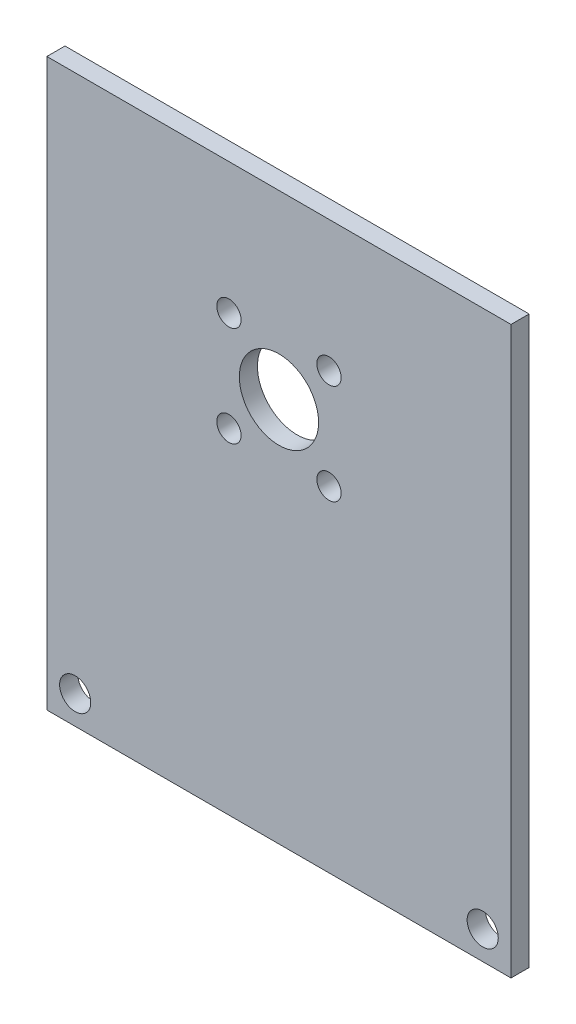
SolidWorks part; units mm, degrees
material "AISI 304"
ref_plane "Front Plane" through (0, 0, 0) normal (0, 0, 1) x (1, 0, 0)
ref_plane "Top Plane" through (0, 0, 0) normal (0, 1, 0) x (1, 0, 0)
ref_plane "Right Plane" through (0, 0, 0) normal (1, 0, 0) x (0, 0, -1)
sketch "Sketch1" plane through (0, 0, 0) normal (0, 0, 1) x (1, 0, 0)
  line L1 (-75, 80) -> (75, 80)
  line L2 (-75, 80) -> (-75, -80)
  line L3 (-75, -80) -> (75, -80)
  line L4 (75, 80) -> (75, -80)
  line L5 (-75, 80) -> (75, -80) construction
  line L6 (-75, -80) -> (75, 80) construction
  point P0 (0, 0)
  dimension "D1" = 150
  dimension "D2" = 160
extrude "Boss-Extrude1" add sketch "Sketch1" along normal blind 3.2
sketch "Sketch2" plane through (0, 0, 3.2) normal (0, 0, 1) x (1, 0, 0)
  line L0 (-75, -80) -> (75, -80) construction
  circle A0 centre (0, -12) radius 7
  circle A1 centre (-36, -75) radius 2.75 construction
  circle A2 centre (36, -75) radius 2.75 construction
  circle A3 centre (-36, -75) radius 2.75
  circle A4 centre (36, -75) radius 2.75
  dimension "D1" = 14
  dimension "D2" = 68
extrude "Cut-Extrude1" cut sketch "Sketch2" against normal up to next
sketch "Sketch3" plane through (0, 0, 3.2) normal (0, 0, 1) x (1, 0, 0)
  line L0 (-83.9315, 71.9315) -> (0, -12) construction
  line L1 (0, -12) -> (-75, -12) construction
  line L2 (-75, 80) -> (-75, -80) construction
  circle A0 centre (-8.8388, -3.1612) radius 2.15
  dimension "D1" = 4.3
  dimension "D2" = 12.5
  dimension "D3" = 45
extrude "Cut-Extrude2" cut sketch "Sketch3" against normal through all
pattern_circular "CirPattern1" count 4 every 90 about axis through (0, -12, 0) along (0, 0, 1) of "Cut-Extrude2"
sketch "Sketch5" plane through (0, 0, 3.2) normal (0, 0, 1) x (1, 0, 0)
  line L0 (-75, -80) -> (75, -80) construction
  line L1 (-41, -80) -> (41, -80)
  line L2 (-41, 20) -> (41, 20)
  line L5 (41, -80) -> (41, 20)
  line L7 (-41, 20) -> (-41, -80)
  dimension "D1" = 82
  dimension "D2" = 100
extrude "Cut-Extrude4" cut sketch "Sketch5" against normal blind 10 flip side to cut
sketch "Sketch6" plane through (0, 0, 3.2) normal (0, 0, 1) x (1, 0, 0)
  line L0 (0, -12) -> (0, 29) construction
